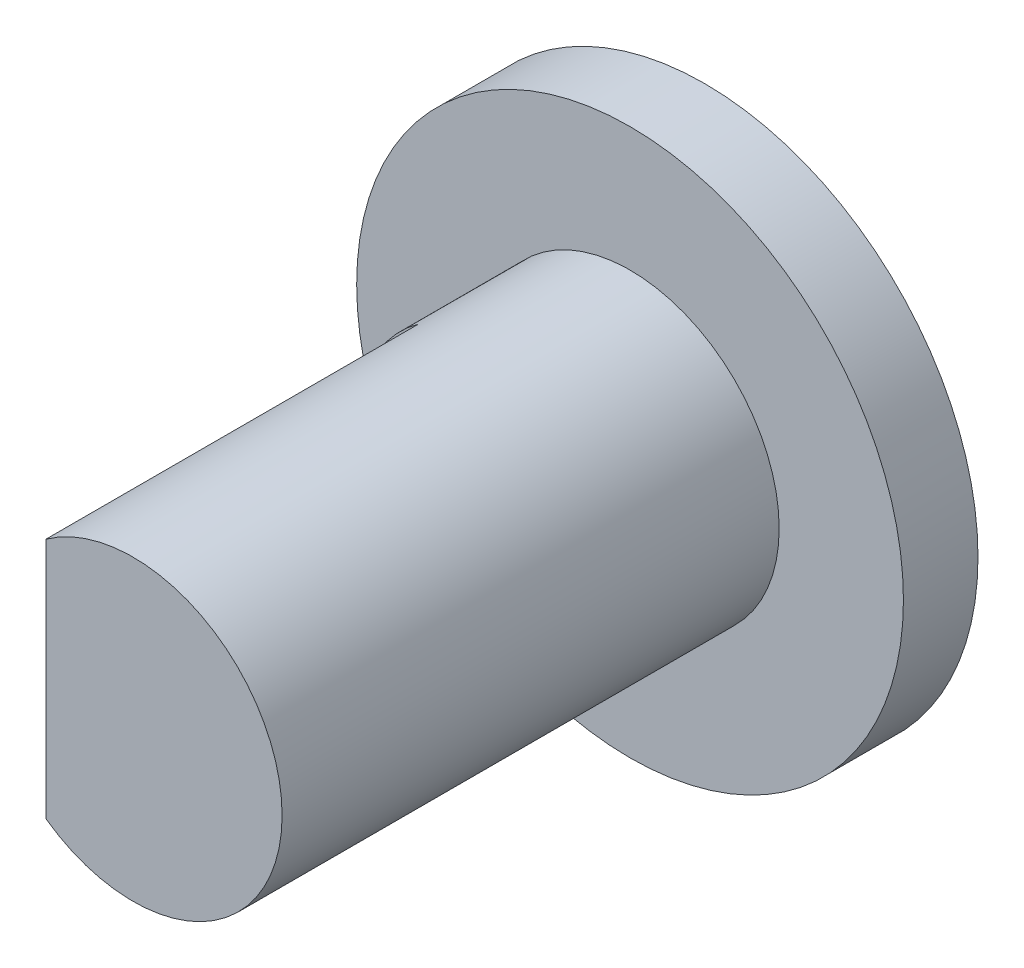
SolidWorks part; units mm, degrees
ref_plane "Front" through (0, 0, 0) normal (0, 0, 1) x (1, 0, 0)
ref_plane "Top" through (0, 0, 0) normal (0, 1, 0) x (1, 0, 0)
ref_plane "Right" through (0, 0, 0) normal (1, 0, 0) x (0, 0, -1)
sketch "Sketch1" plane through (0, 0, 0) normal (0, 0, 1) x (1, 0, 0)
  circle A0 centre (0, 0) radius 11
  dimension "D1" = 22
extrude "Boss-Extrude1" add sketch "Sketch1" along normal blind 3
sketch "Sketch2" plane through (0, 0, 3) normal (0, 0, 1) x (1, 0, 0)
  circle A0 centre (0, 0) radius 6
  dimension "D1" = 12
extrude "Boss-Extrude2" add sketch "Sketch2" along normal blind 20
sketch "Sketch3" plane through (0, 0, 23) normal (0, 0, 1) x (1, 0, 0)
  line L0 (-3.5, 4.8734) -> (-3.5, -4.8734)
  circle A0 centre (0, 0) radius 6 construction
  arc A1 (-3.5, 4.8734) -> (-3.5, -4.8734) centre (0, 0) ccw
  point P5 (-3.5, 0)
  dimension "D1" = 3.5
extrude "Cut-Extrude1" cut sketch "Sketch3" against normal blind 15
